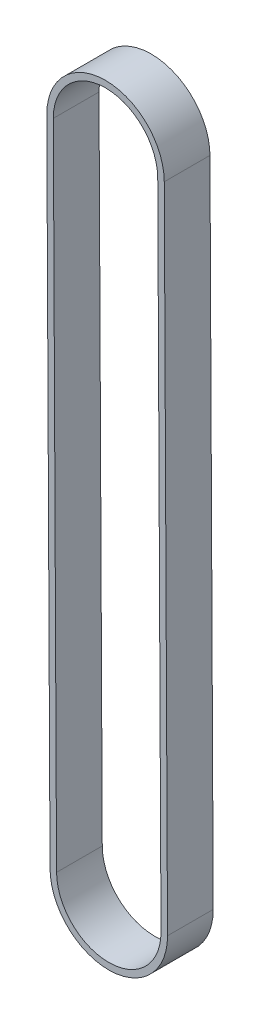
SolidWorks part; units mm, degrees
ref_plane "Front Plane" through (0, 0, 0) normal (0, 0, 1) x (1, 0, 0)
ref_plane "Top Plane" through (0, 0, 0) normal (0, 1, 0) x (1, 0, 0)
ref_plane "Right Plane" through (0, 0, 0) normal (1, 0, 0) x (0, 0, -1)
sketch "Sketch2" plane through (0, 0, 0) normal (0, 0, 1) x (1, 0, 0)
  line L0 (0, 0) -> (1, 0) construction
  line L1 (0, 0) -> (0, 1) construction
  line L2 (7.9999, 0.0401) -> (8.4999, -99.7499)
  line L3 (-7.4999, -99.8301) -> (-7.9999, -0.0401)
  arc A0 (-7.9999, -0.0401) -> (7.9999, 0.0401) centre (0, 0) cw
  arc A1 (8.4999, -99.7499) -> (-7.4999, -99.8301) centre (0.5, -99.79) cw
extrude "Extrude-Thin1" add sketch "Sketch2" along normal mid plane 7 from offset 3.5 thin offset against normal yes
